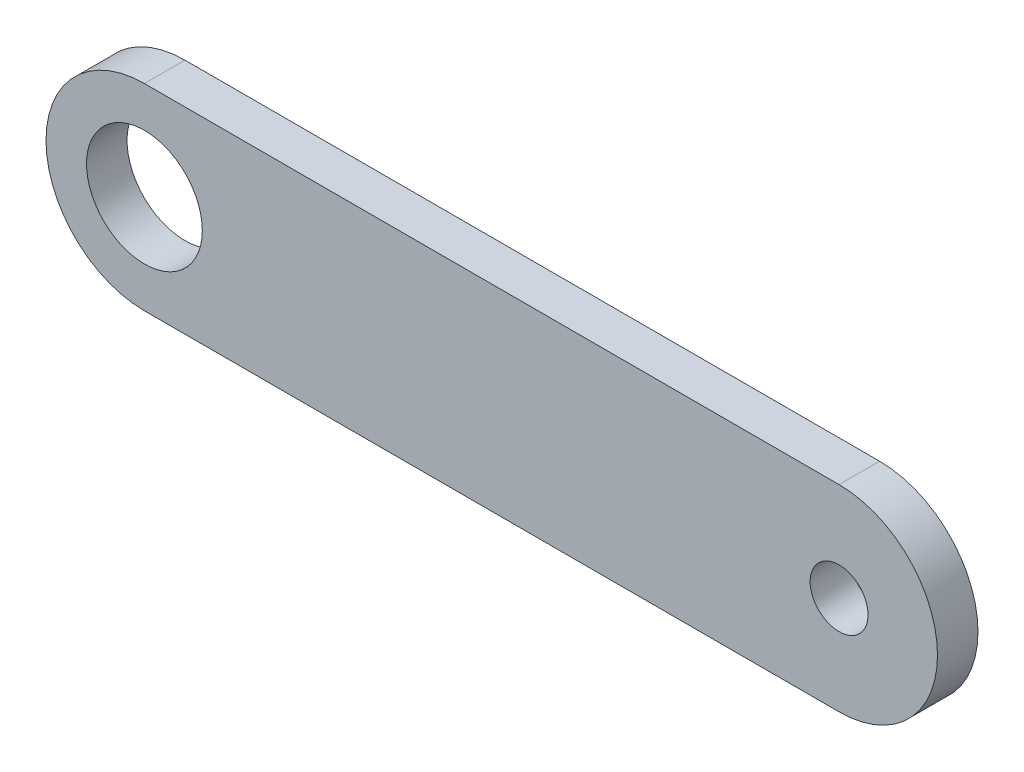
SolidWorks part; units mm, degrees
material "普通碳钢"
ref_plane "前视基准面" through (0, 0, 0) normal (0, 0, 1) x (1, 0, 0)
ref_plane "上视基准面" through (0, 0, 0) normal (0, 1, 0) x (1, 0, 0)
ref_plane "右视基准面" through (0, 0, 0) normal (1, 0, 0) x (0, 0, -1)
sketch "草图1" plane through (0, 0, 0) normal (0, 0, 1) x (1, 0, 0)
  line L0 (30, 0) -> (-30, 0) construction
  line L1 (30, 8.5) -> (-30, 8.5)
  line L2 (30, -8.5) -> (-30, -8.5)
  circle A0 centre (30, 0) radius 2.5
  circle A1 centre (-30, 0) radius 5
  arc A2 (30, 8.5) -> (30, -8.5) centre (30, 0) cw
  arc A3 (-30, 8.5) -> (-30, -8.5) centre (-30, 0) ccw
  point P2 (0, 0)
  dimension "D2" = 10
  dimension "D3" = 5
  dimension "D1" = 60
  dimension "D4" = 8.5
extrude "凸台-拉伸1" add sketch "草图1" along normal blind 3.5
